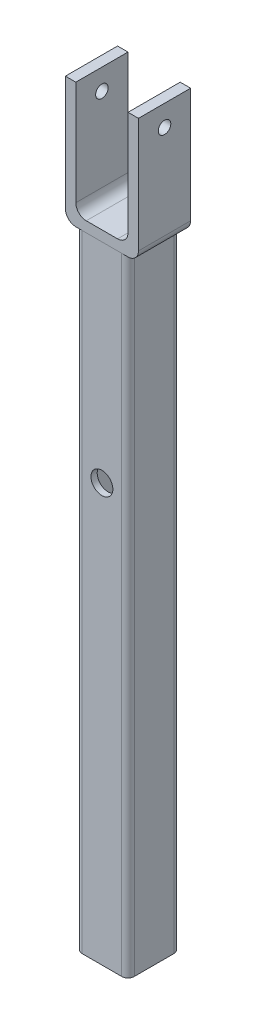
SolidWorks part; units mm, degrees
ref_plane "Front Plane" through (0, 0, 0) normal (0, 0, 1) x (1, 0, 0)
ref_plane "Top Plane" through (0, 0, 0) normal (0, 1, 0) x (1, 0, 0)
ref_plane "Right Plane" through (0, 0, 0) normal (1, 0, 0) x (0, 0, -1)
sketch "Sketch1" plane through (0, 0, 0) normal (0, 1, 0) x (1, 0, 0)
  line L15 (9.5, 12.5) -> (-9.5, 12.5)
  line L16 (12.5, 9.5) -> (12.5, -9.5)
  line L17 (9.5, -12.5) -> (-9.5, -12.5)
  line L18 (-12.5, 9.5) -> (-12.5, -9.5)
  line L19 (12.5, 12.5) -> (-12.5, -12.5) construction
  line L20 (12.5, -12.5) -> (-12.5, 12.5) construction
  line L21 (-6.5, 9.5) -> (6.5, 9.5)
  line L22 (-9.5, 6.5) -> (-9.5, -6.5)
  line L23 (-6.5, -9.5) -> (6.5, -9.5)
  line L24 (9.5, 6.5) -> (9.5, -6.5)
  line L25 (-9.5, 9.5) -> (9.5, -9.5) construction
  line L26 (-9.5, -9.5) -> (9.5, 9.5) construction
  arc A0 (9.5, 6.5) -> (6.5, 9.5) centre (6.5, 6.5) ccw
  arc A1 (9.5, -6.5) -> (6.5, -9.5) centre (6.5, -6.5) cw
  arc A2 (-6.5, -9.5) -> (-9.5, -6.5) centre (-6.5, -6.5) cw
  arc A3 (12.5, 9.5) -> (9.5, 12.5) centre (9.5, 9.5) ccw
  arc A4 (-9.5, 6.5) -> (-6.5, 9.5) centre (-6.5, 6.5) cw
  arc A5 (9.5, -12.5) -> (12.5, -9.5) centre (9.5, -9.5) ccw
  arc A6 (-9.5, -12.5) -> (-12.5, -9.5) centre (-9.5, -9.5) cw
  arc A7 (-12.5, 9.5) -> (-9.5, 12.5) centre (-9.5, 9.5) cw
  point P0 (0, 0)
  point P6 (0, 0)
  dimension "D5" = 3
  dimension "D6" = 3
  dimension "D7" = 3
  dimension "D8" = 3
  dimension "D9" = 3
  dimension "D10" = 3
  dimension "D11" = 3
  dimension "D1" = 19
  dimension "D2" = 19
  dimension "D3" = 25
  dimension "D4" = 25
extrude "Boss-Extrude1" add sketch "Sketch1" along normal blind 300
sketch "Sketch2" plane through (0, 0, -12.5) normal (0, 0, -1) x (-1, 0, 0)
  line L0 (0, 0) -> (0, 200)
  line L1 (-9.5, 0) -> (9.5, 0) construction
  circle A0 centre (0, 200) radius 7.5
  dimension "D2" = 15
  dimension "D1" = 200
extrude "Cut-Extrude1" cut sketch "Sketch2" against normal blind 3 contours A0
sketch "Sketch3" plane through (0, 0, 12.5) normal (0, 0, 1) x (1, 0, 0)
  line L0 (0, 0) -> (0, 200)
  line L1 (-9.5, 0) -> (9.5, 0) construction
  circle A0 centre (0, 200) radius 5.25
  dimension "D1" = 10.5
extrude "Cut-Extrude2" cut sketch "Sketch3" against normal blind 3 contours A0
sketch "Sketch5" plane through (0, 300, 0) normal (0, 1, 0) x (1, 0, 0)
  line L1 (17.5, 12.5) -> (-17.5, 12.5)
  line L2 (17.5, 12.5) -> (17.5, -12.5)
  line L3 (17.5, -12.5) -> (-17.5, -12.5)
  line L4 (-17.5, 12.5) -> (-17.5, -12.5)
  line L5 (17.5, 12.5) -> (-17.5, -12.5) construction
  line L6 (17.5, -12.5) -> (-17.5, 12.5) construction
  point P0 (0, 0)
  dimension "D1" = 25
  dimension "D2" = 35
extrude "Boss-Extrude2" add sketch "Sketch5" along normal blind 60 separate body
sketch "Sketch6" plane through (0, 360, 0) normal (0, 1, 0) x (1, 0, 0)
sketch "Sketch7" plane through (0, 360, 0) normal (0, 1, 0) x (1, 0, 0)
  line L0 (17.5, 12.5) -> (-17.5, 12.5) construction
  line L1 (12.5, -12.5) -> (-12.5, -12.5)
  line L2 (12.5, -12.5) -> (12.5, 12.5)
  line L3 (12.5, 12.5) -> (-12.5, 12.5)
  line L4 (-12.5, -12.5) -> (-12.5, 12.5)
  line L5 (12.5, -12.5) -> (-12.5, 12.5) construction
  line L6 (12.5, 12.5) -> (-12.5, -12.5) construction
  point P0 (0, 0)
extrude "Cut-Extrude4" cut sketch "Sketch7" against normal blind 55
sketch "Sketch8" plane through (-17.5, 0, 0) normal (-1, 0, 0) x (0, 0, 1)
  line L0 (0, 360) -> (0, 350)
  line L1 (-12.5, 360) -> (12.5, 360) construction
  circle A0 centre (0, 350) radius 3
  dimension "D2" = 6
  dimension "D1" = 10
extrude "Cut-Extrude5" cut sketch "Sketch8" against normal blind 55 contours A0
fillet "Fillet1" radius 5 2 edges at (12.5, 305, 0) (-12.5, 305, 0)
fillet "Fillet2" radius 5 2 edges at (17.5, 300, 0) (-17.5, 300, 0)
sketch "Sketch9" plane through (12.5, 0, 0) normal (1, 0, 0) x (0, 0, -1)
  line L0 (0, 0) -> (0, 150)
  line L1 (-9.5, 0) -> (9.5, 0) construction
  circle A0 centre (0, 150) radius 3
